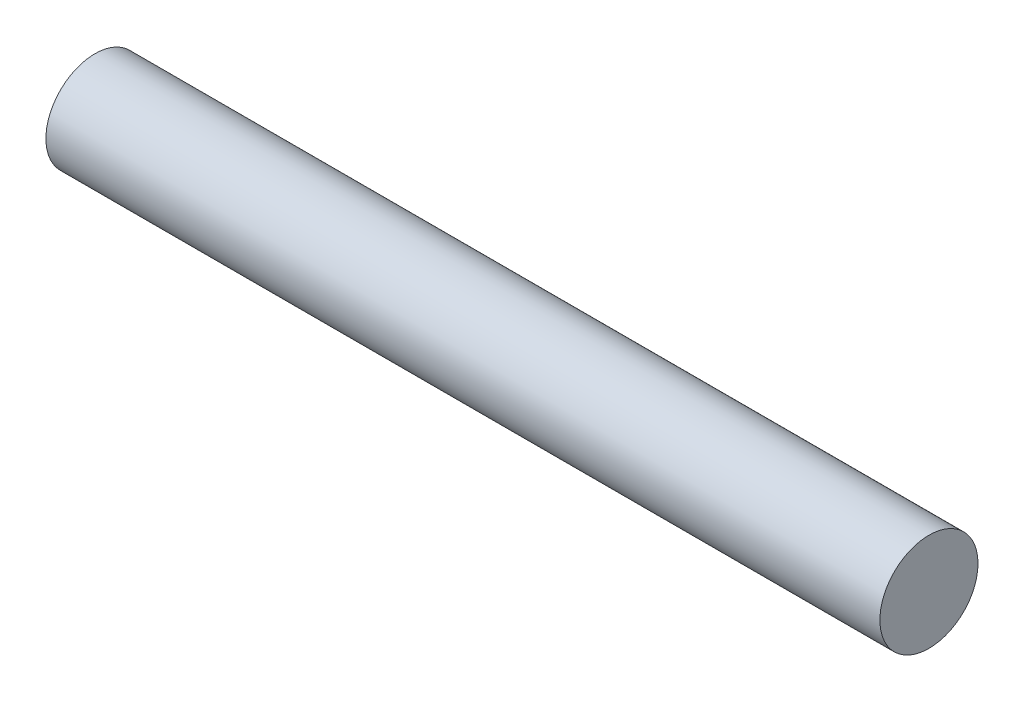
SolidWorks part; units mm, degrees
ref_plane "Front Plane" through (0, 0, 0) normal (0, 0, 1) x (1, 0, 0)
ref_plane "Top Plane" through (0, 0, 0) normal (0, 1, 0) x (1, 0, 0)
ref_plane "Right Plane" through (0, 0, 0) normal (1, 0, 0) x (0, 0, -1)
sketch "Sketch1" plane through (0, 0, 0) normal (1, 0, 0) x (0, 0, -1)
  circle A0 centre (-11.6388, 3.3142) radius 10
  dimension "D1" = 20
extrude "Boss-Extrude1" add sketch "Sketch1" along normal mid plane 170
